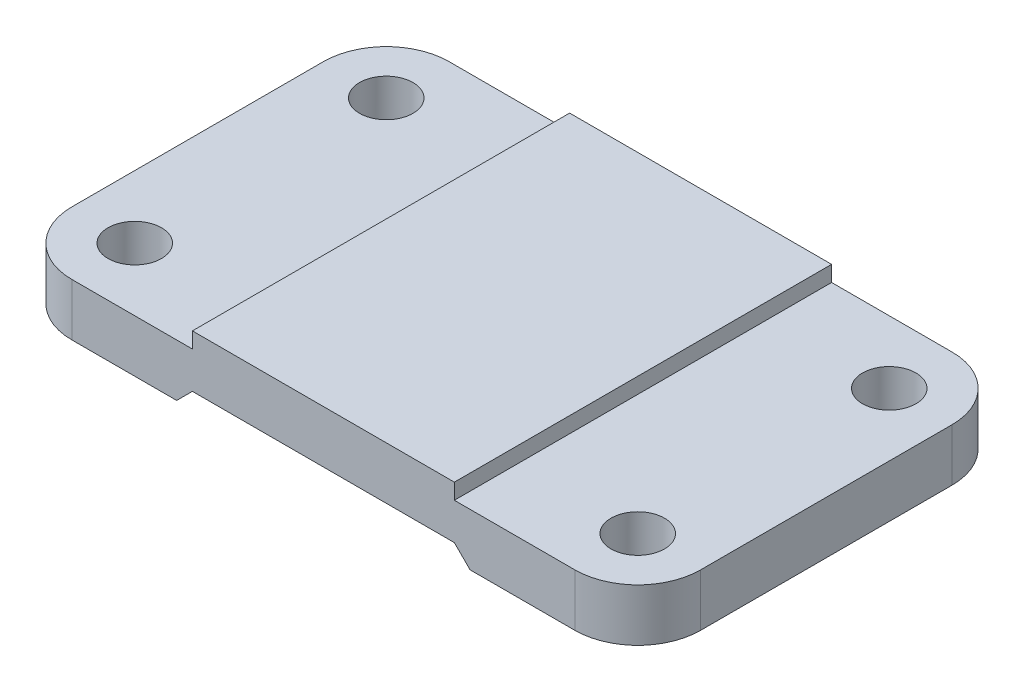
SolidWorks part; units mm, degrees
ref_plane "Front Plane" through (0, 0, 0) normal (0, 0, 1) x (1, 0, 0)
ref_plane "Top Plane" through (0, 0, 0) normal (0, 1, 0) x (1, 0, 0)
ref_plane "Right Plane" through (0, 0, 0) normal (1, 0, 0) x (0, 0, -1)
sketch "Sketch1" plane through (0, 0, 0) normal (0, 1, 0) x (1, 0, 0)
  line L1 (-60, -36) -> (60, -36)
  line L2 (-60, -36) -> (-60, 36)
  line L3 (-60, 36) -> (60, 36)
  line L4 (60, -36) -> (60, 36)
  line L5 (-60, -36) -> (60, 36) construction
  line L6 (-60, 36) -> (60, -36) construction
  point P0 (0, 0)
  dimension "D1" = 120
  dimension "D2" = 72
extrude "Boss-Extrude1" add sketch "Sketch1" along normal blind 10
fillet "Fillet1" radius 12 4 edges at (-60, 5, -36) (-60, 5, 36) (60, 5, -36) (60, 5, 36)
hole_wizard "M12 Tapped Hole1" positions "Sketch2" profile "Sketch3" tap size "M12" standard "DIN" end condition up to next
sketch "Sketch2" plane through (0, 10, 0) normal (0, 1, 0) x (1, 0, 0)
  point P0 (48, -24)
  point P3 (48, 24)
  point P6 (-48, 24)
  point P9 (-48, -24)
sketch "Sketch3" plane through (48, 10, 24) normal (1, 0, 0) x (0, 0, 1)
  line L0 (0, 0) -> (0, 10)
  line L1 (0, 10) -> (5.1, 10)
  line L2 (5.1, 10) -> (5.1, 0)
  line L5 (5.1, 0) -> (0, 0)
  line L11 (0, -6.35) -> (0, 107.95) construction
  dimension "Thru Tap Drill Dia." = 10.2
  dimension "Thru Tap Drill Depth" = 10
cosmetic thread "Hole Thread1" parameters "D2"=12
cosmetic thread "Hole Thread2" parameters "D2"=12
cosmetic thread "Hole Thread3" parameters "D2"=12
cosmetic thread "Hole Thread4" parameters "D2"=12
sketch "Sketch4" plane through (0, 10, 0) normal (0, 1, 0) x (1, 0, 0)
  line L0 (48, 36) -> (-48, 36) construction
  line L1 (25, -36) -> (-25, -36)
  line L2 (25, -36) -> (25, 36)
  line L3 (25, 36) -> (-25, 36)
  line L4 (-25, -36) -> (-25, 36)
  line L5 (25, -36) -> (-25, 36) construction
  line L6 (25, 36) -> (-25, -36) construction
  point P0 (0, 0)
  dimension "D1" = 50
extrude "Boss-Extrude2" add sketch "Sketch4" along normal blind 3
sketch "Sketch5" plane through (0, 0, 36) normal (0, 0, 1) x (1, 0, 0)
  line L0 (0, 0) -> (0, 3) construction
  line L1 (-48, 0) -> (48, 0) construction
  line L2 (-28, 0) -> (-25, 3)
  line L3 (-25, 3) -> (25, 3)
  line L4 (25, 3) -> (28, 0)
  line L5 (28, 0) -> (-28, 0)
  point P9 (0, 0)
  dimension "D1" = 45
  dimension "D2" = 56
  dimension "D3" = 3
extrude "Cut-Extrude1" cut sketch "Sketch5" against normal through all
